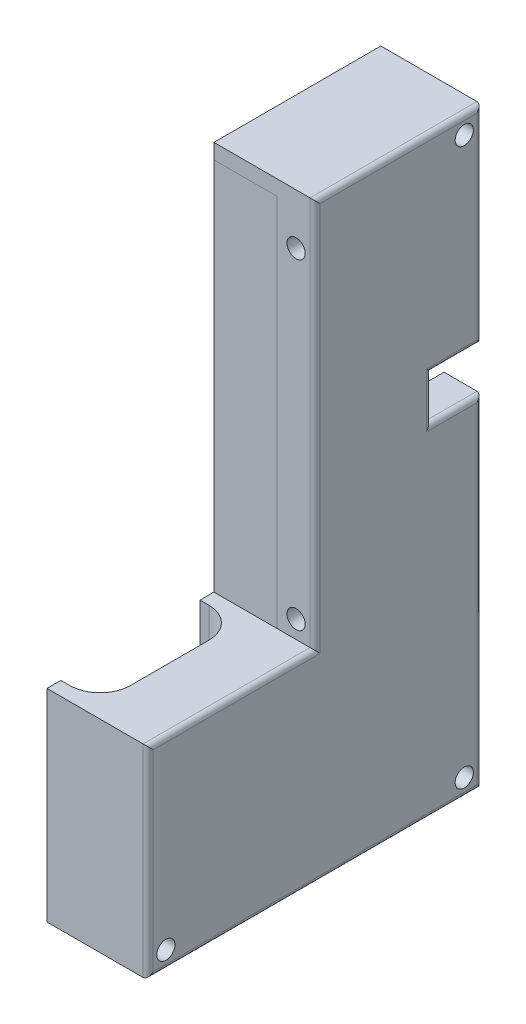
SolidWorks part; units mm, degrees
material "ABS"
ref_plane "Front" through (0, 0, 0) normal (0, 0, 1) x (1, 0, 0)
ref_plane "Top" through (0, 0, 0) normal (0, 1, 0) x (1, 0, 0)
ref_plane "Right" through (0, 0, 0) normal (1, 0, 0) x (0, 0, -1)
sketch "ｽｹｯﾁ1" plane through (0, 0, 0) normal (1, 0, 0) x (0, 0, -1)
  line L0 (23, 92) -> (0, 92)
  line L1 (33, 92) -> (23, 92)
  line L2 (33, 92) -> (33, -25)
  line L3 (33, -25) -> (23, -25)
  line L4 (23, 92) -> (23, -25)
  line L5 (0, 92) -> (0, -25)
  line L6 (0, -25) -> (23, -25)
  line L7 (0, -25) -> (-33, -25)
  line L8 (-33, -25) -> (-33, 0)
  line L9 (-33, 0) -> (0, 0)
  dimension "D1" = 117
  dimension "D2" = 10
  dimension "D3" = 33
  dimension "D4" = 23
  dimension "D5" = 25
extrude "ﾎﾞｽ - 押し出し1" add sketch "ｽｹｯﾁ1" along normal blind 60 contours L9 L8 L7 L5 | L5 L6 L4 L0 | L1 L4 L3 L2
sketch "ｽｹｯﾁ2" plane through (0, 0, -33) normal (0, 0, -1) x (-1, 0, 0)
  line L0 (-60, 92) -> (-60, -25) construction
  line L1 (-7.5, 22.5) -> (-52.5, 22.5)
  line L2 (-7.5, 22.5) -> (-7.5, 84.5)
  line L3 (-7.5, 84.5) -> (-52.5, 84.5)
  line L4 (-52.5, 22.5) -> (-52.5, 84.5)
  line L5 (-7.5, 22.5) -> (-52.5, 84.5) construction
  line L6 (-7.5, 84.5) -> (-52.5, 22.5) construction
  line L8 (0, 92) -> (0, -25) construction
  line L9 (-60, 92) -> (0, 92) construction
  point P0 (-30, 53.5)
  dimension "D1" = 62
  dimension "D2" = 7.5
  dimension "D3" = 7.5
  dimension "D4" = 7.5
extrude "ｶｯﾄ - 押し出し1" cut sketch "ｽｹｯﾁ2" against normal blind 10
sketch "ｽｹｯﾁ3" plane through (0, 92, 0) normal (0, 1, 0) x (1, 0, 0)
  line L1 (0, 33) -> (0, 0) construction
  line L2 (60, 0) -> (0, 0) construction
  circle A0 centre (29, 12.5) radius 8.1
  dimension "D1" = 16.2
  dimension "D2" = 29
  dimension "D3" = 12.5
extrude "ｶｯﾄ - 押し出し2" cut sketch "ｽｹｯﾁ3" against normal blind 10
sketch "ｽｹｯﾁ4" plane through (0, 0, -33) normal (0, 0, -1) x (-1, 0, 0)
  line L0 (-60, -25) -> (0, -25) construction
  line L1 (-7.5, 22.5) -> (-52.5, 22.5)
  line L2 (-7.5, 22.5) -> (-7.5, -17.5)
  line L3 (-7.5, -17.5) -> (-52.5, -17.5)
  line L4 (-52.5, 22.5) -> (-52.5, -17.5)
  line L7 (-60, 92) -> (-60, -25) construction
  dimension "D1" = 7.5
  dimension "D2" = 7.5
extrude "ｶｯﾄ - 押し出し3" cut sketch "ｽｹｯﾁ4" against normal offset from surface (58.5 mm away) 7.5 up to face at (30, -12.5, 33)
sketch "ｽｹｯﾁ5" plane through (0, 0, 0) normal (0, 1, 0) x (1, 0, 0)
  line L1 (41.75, -2.75) -> (16.25, -2.75)
  line L2 (47.75, -8.75) -> (47.75, -24.25)
  line L3 (41.75, -30.25) -> (16.25, -30.25)
  line L4 (10.25, -8.75) -> (10.25, -24.25)
  line L5 (47.75, -2.75) -> (10.25, -30.25) construction
  line L6 (47.75, -30.25) -> (10.25, -2.75) construction
  line L7 (0, -33) -> (0, 0) construction
  line L11 (60, -33) -> (0, -33)
  line L12 (60, -33) -> (60, 0)
  line L13 (60, 0) -> (0, 0)
  line L14 (0, -33) -> (0, 0)
  arc A0 (10.25, -8.75) -> (16.25, -2.75) centre (16.25, -8.75) cw
  arc A1 (47.75, -8.75) -> (41.75, -2.75) centre (41.75, -8.75) ccw
  arc A2 (47.75, -24.25) -> (41.75, -30.25) centre (41.75, -24.25) cw
  arc A3 (16.25, -30.25) -> (10.25, -24.25) centre (16.25, -24.25) cw
  point P0 (29, -16.5)
  dimension "D5" = 6
  dimension "D1" = 27.5
  dimension "D2" = 37.5
  dimension "D3" = 29
  dimension "D4" = 2.75
extrude "ﾎﾞｽ - 押し出し2" add sketch "ｽｹｯﾁ5" along normal blind 15
sketch "ｽｹｯﾁ6" plane through (0, 0, 0) normal (0, 1, 0) x (1, 0, 0)
  line L20 (34.75, -30.25) -> (34.75, -2.75)
  line L21 (42.75, -30.25) -> (42.75, -2.8339)
  line L22 (34.75, -25.5) -> (42.75, -25.5)
  line L24 (41.75, -2.75) -> (16.25, -2.75)
  line L25 (47.75, -24.25) -> (47.75, -8.75)
  line L26 (16.25, -30.25) -> (41.75, -30.25)
  line L27 (10.25, -8.75) -> (10.25, -24.25)
  line L28 (41.75, -2.75) -> (16.25, -2.75)
  line L29 (47.75, -24.25) -> (47.75, -8.75)
  line L30 (16.25, -30.25) -> (41.75, -30.25)
  line L31 (10.25, -8.75) -> (10.25, -24.25)
  line L32 (34.75, -7.5) -> (42.75, -7.5)
  arc A21 (16.25, -2.75) -> (10.25, -8.75) centre (16.25, -8.75) ccw
  arc A22 (47.75, -8.75) -> (41.75, -2.75) centre (41.75, -8.75) ccw
  arc A23 (41.75, -30.25) -> (47.75, -24.25) centre (41.75, -24.25) ccw
  arc A24 (10.25, -24.25) -> (16.25, -30.25) centre (16.25, -24.25) ccw
  arc A25 (16.25, -2.75) -> (10.25, -8.75) centre (16.25, -8.75) ccw
  arc A26 (47.75, -8.75) -> (41.75, -2.75) centre (41.75, -8.75) ccw
  arc A27 (41.75, -30.25) -> (47.75, -24.25) centre (41.75, -24.25) ccw
  arc A28 (10.25, -24.25) -> (16.25, -30.25) centre (16.25, -24.25) ccw
  arc M14 (10.3817, -25.5) -> (16.25, -30.25) centre (16.25, -24.25) ccw
  line M15 (16.25, -30.25) -> (41.75, -30.25)
  arc M16 (41.75, -30.25) -> (47.6183, -25.5) centre (41.75, -24.25) ccw
  line M17 (47.6183, -25.5) -> (10.3817, -25.5)
  dimension "D2" = 13
  dimension "D3" = 8
  dimension "D4" = 18
  dimension "D5" = 4.75
  dimension "D1" = 0
extrude "ﾎﾞｽ - 押し出し3" add sketch "ｽｹｯﾁ6" along normal blind 7 contours L31 A28 L20 L28 A25 M17 | L20 M15 M17 M14 | L21 L20 M16 M17 M15 | A27 L29 A26 L21 M17 | L21 M16 M17 | L21 A26 L28 L20 L32
sketch "ｽｹｯﾁ7" plane through (0, 0, 0) normal (0, 0, 1) x (1, 0, 0)
  line L0 (0, 92) -> (0, 15) construction
  line L1 (52.5, 89) -> (7.5, 89)
  line L2 (52.5, 89) -> (52.5, 22.5)
  line L3 (52.5, 22.5) -> (7.5, 22.5)
  line L4 (7.5, 89) -> (7.5, 22.5)
  line L5 (52.5, 89) -> (7.5, 22.5) construction
  line L6 (52.5, 22.5) -> (7.5, 89) construction
  line L7 (60, 92) -> (0, 92) construction
  line L9 (52.5, 22.5) -> (7.5, 22.5) construction
  line L11 (52.5, 22.5) -> (52.5, 15) construction
  point P0 (30, 55.75)
  dimension "D1" = 7.5
  dimension "D2" = 3
extrude "ｶｯﾄ - 押し出し4" cut sketch "ｽｹｯﾁ7" against normal offset from surface (20 mm away) 3 up to face at (30, 53.5, -23)
sketch "ｽｹｯﾁ8" plane through (0, 89, 0) normal (0, -1, 0) x (-1, 0, 0)
  line L1 (-7.5, 0) -> (-52.5, 0)
  line L2 (-7.5, 0) -> (-7.5, 2)
  line L3 (-7.5, 2) -> (-52.5, 2)
  line L4 (-52.5, 0) -> (-52.5, 2)
  line L6 (-52.5, 20) -> (-52.5, 0) construction
  dimension "D1" = 2
extrude "ﾎﾞｽ - 押し出し4" add sketch "ｽｹｯﾁ8" along normal up to vertex (89 mm away) separate body
sketch "ｽｹｯﾁ9" plane through (0, 0, 0) normal (-1, 0, 0) x (0, 0, 1)
  line L0 (-33, 92) -> (0, 92) construction
  line L1 (-33, 92) -> (-33, -25) construction
  line L2 (-33, -25) -> (33, -25) construction
  line L3 (33, -25) -> (33, 15) construction
  circle A0 centre (-29.5, 88.5) radius 1.8
  circle A1 centre (-29.5, -21.5) radius 1.8
  circle A2 centre (29.5, -21.5) radius 1.8
  dimension "D3" = 3.6
  dimension "D5" = 3.5
  dimension "D1" = 3.5
  dimension "D2" = 3.5
  dimension "D4" = 3.5
extrude "ｶｯﾄ - 押し出し5" cut sketch "ｽｹｯﾁ9" against normal through all
sketch "ｽｹｯﾁ10" plane through (0, 0, 0) normal (0, 0, 1) x (1, 0, 0)
  line L0 (60, 92) -> (0, 92) construction
  line L1 (7.5, 15) -> (0, 15) construction
  line L2 (0, 92) -> (0, 15) construction
  line L3 (60, 92) -> (60, 15) construction
  circle A0 centre (3.75, 82) radius 1.8
  circle A1 centre (56.25, 82) radius 1.8
  circle A2 centre (56.25, 18.5) radius 1.8
  circle A3 centre (3.75, 18.5) radius 1.8
  dimension "D3" = 3.6
  dimension "D1" = 3.5
  dimension "D2" = 10
  dimension "D4" = 3.75
  dimension "D5" = 3.75
extrude "ｶｯﾄ - 押し出し6" cut sketch "ｽｹｯﾁ10" against normal through all both and the other way through all
sketch "ｽｹｯﾁ12" plane through (0, 0, -23) normal (0, 0, -1) x (-1, 0, 0)
  line L0 (-52.5, 84.5) -> (-52.5, 22.5) construction
  line L2 (-7.5, 84.5) -> (-52.5, 84.5) construction
  circle A0 centre (-49, 81.5) radius 1.8
  circle A1 centre (-11, 81.5) radius 1.8
  circle A2 centre (-11, 39.5) radius 1.8
  circle A3 centre (-49, 39.5) radius 1.8
  dimension "D3" = 3.6
  dimension "D1" = 42
  dimension "D2" = 38
  dimension "D4" = 3.5
  dimension "D5" = 3
extrude "ｶｯﾄ - 押し出し7" cut sketch "ｽｹｯﾁ12" against normal up to next (3 mm away)
sketch "ｽｹｯﾁ19" plane through (0, 0, 0) normal (-1, 0, 0) x (0, 0, 1)
  line L12 (33, -25) -> (33, 15)
  line L13 (33, 15) -> (0, 15)
  line L14 (0, 15) -> (0, 92)
  line L15 (0, 92) -> (-33, 92)
  line L16 (-33, 92) -> (-33, -25)
  line L17 (-33, -25) -> (33, -25)
  line L18 (33, -25) -> (33, 15)
  line L19 (33, 15) -> (0, 15)
  line L20 (0, 15) -> (0, 92)
  line L21 (0, 92) -> (-33, 92)
  line L22 (-33, 92) -> (-33, -25)
  line L23 (-33, -25) -> (33, -25)
  dimension "D1" = 0
extrude "ｶｯﾄ - 押し出し8" cut sketch "ｽｹｯﾁ19" against normal blind 40
sketch "ｽｹｯﾁ21" plane through (40, 0, 0) normal (-1, 0, 0) x (0, 0, 1)
  line L0 (-20, 22.5) -> (-20, 89) construction
  line L1 (-23, 84.5) -> (-20, 84.5)
  line L2 (-23, 84.5) -> (-23, 22.5)
  line L3 (-23, 22.5) -> (-20, 22.5)
  line L4 (-20, 84.5) -> (-20, 22.5)
  line L5 (-23, 22.5) -> (-20, 22.5) construction
extrude "ｶｯﾄ - 押し出し9" cut sketch "ｽｹｯﾁ21" against normal offset from surface (5.5 mm away) 7 up to face at (52.5, 33.8182, -9.1818)
sketch "ｽｹｯﾁ23" plane through (0, 0, -33) normal (0, 0, -1) x (-1, 0, 0)
  line L0 (-60, 92) -> (-60, -25) construction
  line L1 (-60, 42.4) -> (-52.5, 42.4)
  line L2 (-60, 42.4) -> (-60, 51.2)
  line L3 (-60, 51.2) -> (-52.5, 51.2)
  line L4 (-52.5, 42.4) -> (-52.5, 51.2)
  line L5 (-52.5, 84.5) -> (-52.5, -17.5) construction
  circle A0 centre (-49, 39.5) radius 1.8 construction
  dimension "D1" = 2.9
  dimension "D2" = 8.8
extrude "ｶｯﾄ - 押し出し10" cut sketch "ｽｹｯﾁ23" against normal up to vertex (10 mm away) up to point (52.5, 22.5, -23)
fillet "ﾌｨﾚｯﾄ1" radius 1 10 edges at (60, 46.8, -23) (60, 42.4, -28) (60, 8.7, -33) (60, -25, 0) (60, -5, 33) (60, 15, 16.5) (60, 53.5, 0) (60, 92, -16.5) (60, 71.6, -33) (60, 51.2, -28)
sketch "ｽｹｯﾁ24" plane through (40, 0, 0) normal (-1, 0, 0) x (0, 0, 1)
  line L0 (-33, -25) -> (33, -25) construction
  line L1 (25.5, -17.5) -> (-25.5, -17.5)
  line L2 (25.5, -17.5) -> (25.5, -22)
  line L3 (25.5, -22) -> (-25.5, -22)
  line L4 (-25.5, -17.5) -> (-25.5, -22)
  line L6 (-33, -17.5) -> (-33, -25) construction
  dimension "D1" = 3
  dimension "D2" = 7.5
extrude "ｶｯﾄ - 押し出し11" cut sketch "ｽｹｯﾁ24" against normal up to vertex
